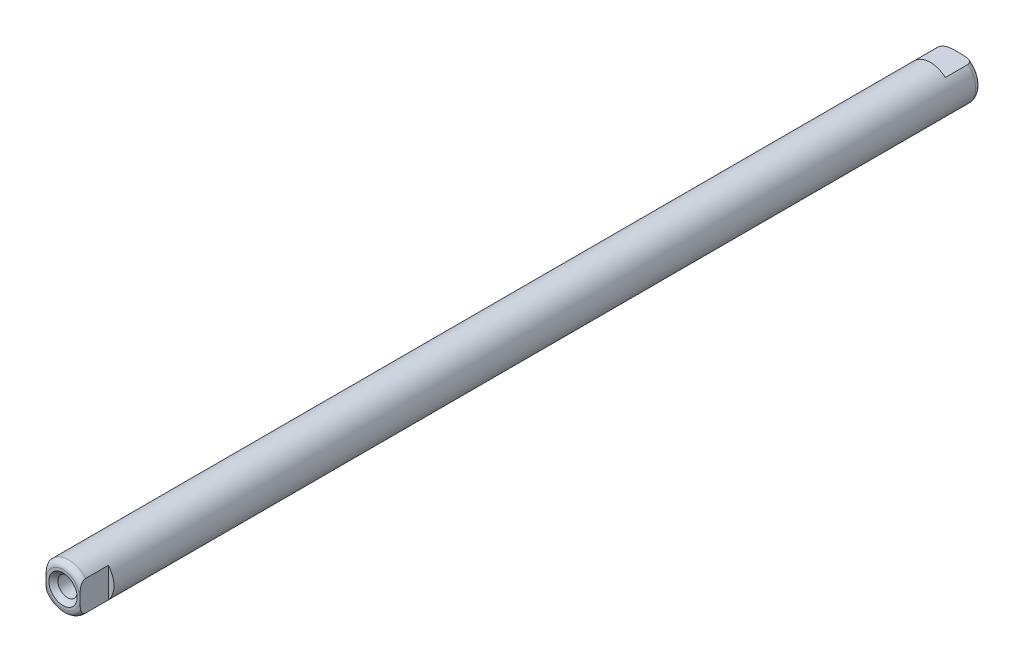
SolidWorks part; units mm, degrees
material "XC38"
ref_plane "Face" through (0, 0, 0) normal (0, 0, 1) x (1, 0, 0)
ref_plane "Dessus" through (0, 0, 0) normal (0, 1, 0) x (1, 0, 0)
ref_plane "Droite" through (0, 0, 0) normal (1, 0, 0) x (0, 0, -1)
sketch "Esquisse1" plane through (0, 0, 0) normal (0, 0, 1) x (1, 0, 0)
  circle A0 centre (0, 0) radius 8
  dimension "D1" = 16
extrude "Boss.-Extru.1" add sketch "Esquisse1" along normal mid plane 316
fillet "Congé1" radius 2 2 edges at (8, 0, -158) (8, 0, 158)
hole_wizard "Trou taraudé M81" positions "Esquisse3" profile "Esquisse2" tap size "M8" standard "ISO"
sketch "Esquisse3" plane through (0, 0, -158) normal (0, 0, -1) x (-1, 0, 0)
  point P0 (0, 0)
sketch "Esquisse2" plane through (0, 0, -158) normal (1, 0, 0) x (0, 1, 0)
  line L0 (0, 0) -> (0, 24.2929)
  line L1 (0, 24.2929) -> (3.4, 22.25)
  line L2 (3.4, 22.25) -> (3.4, 1.6)
  line L3 (3.4, 1.6) -> (5, 0)
  line L5 (5, 0) -> (0, 0)
  line L6 (-3.4, 1.6) -> (-5, 0) construction
  line L10 (0, 24.2929) -> (-3.4, 22.25) construction
  line L11 (0, -6.35) -> (0, 107.95) construction
  dimension "Diamètre du trou pour taraudage" = 6.8
  dimension "Profondeur du trou pour taraudage" = 22.25
  dimension "Diamètre du fraisage entrant" = 10
  dimension "Angle du fraisage entrant" = 90
  dimension "Angle de pointe" = 118
cosmetic thread "Filetage de perçage2" parameters "D1"=16, "D2"=8
mirror "Symétrie5" about plane through (0, 0, 0) normal (0, 0, 1) of "Trou taraudé M81"
sketch "Esquisse4" plane through (0, 0, -158) normal (0, 0, -1) x (-1, 0, 0)
  line L0 (0, 6) -> (0, -6) construction
  line L1 (-8, 6) -> (8, 6)
  line L2 (-8, 6) -> (-8, -6)
  line L3 (-8, -6) -> (8, -6)
  line L4 (8, 6) -> (8, -6)
  circle A0 centre (0, 0) radius 8 construction
  dimension "D1" = 12
extrude "Enlèv. mat.-Extru.1" cut sketch "Esquisse4" against normal blind 10 flip side to cut
sketch "Esquisse5" plane through (0, 0, 158) normal (0, 0, 1) x (1, 0, 0)
  line L0 (-6, 0) -> (6, 0) construction
  line L1 (-6, 8) -> (6, 8)
  line L2 (-6, 8) -> (-6, -8)
  line L3 (-6, -8) -> (6, -8)
  line L4 (6, 8) -> (6, -8)
  circle A0 centre (0, 0) radius 8 construction
  dimension "D1" = 12
extrude "Enlèv. mat.-Extru.2" cut sketch "Esquisse5" against normal blind 10 flip side to cut
